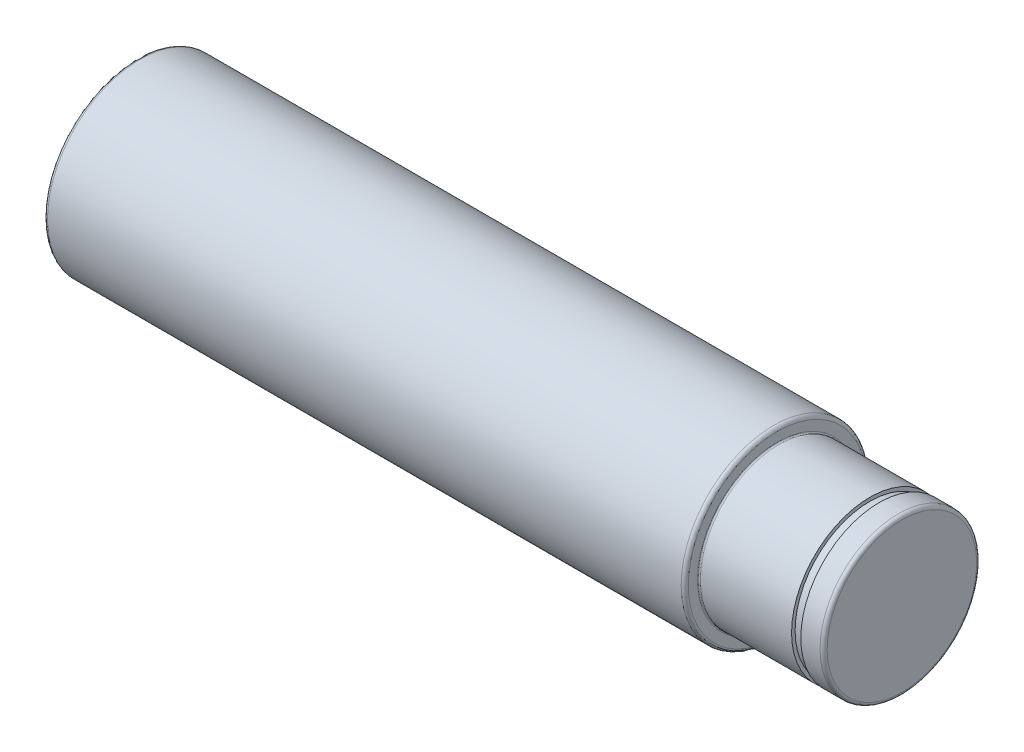
SolidWorks part; units mm, degrees
ref_plane "Plane1" through (0, 0, 0) normal (0, 0, 1) x (1, 0, 0)
ref_plane "Plane2" through (0, 0, 0) normal (0, 1, 0) x (1, 0, 0)
ref_plane "Plane3" through (0, 0, 0) normal (1, 0, 0) x (0, 0, -1)
sketch "Sketch1" plane through (0, 0, 0) normal (0, 0, 1) x (1, 0, 0)
  line L0 (0, 0) -> (0, 12.5)
  line L1 (0.5, 13) -> (89.5, 13)
  line L2 (90, 12.5) -> (90, 11.2)
  line L3 (90.2, 11) -> (103, 11)
  line L4 (103, 11) -> (103, 10.5)
  line L5 (103, 10.5) -> (104.3, 10.5)
  line L6 (104.3, 10.5) -> (104.3, 11)
  line L7 (104.3, 11) -> (107, 11)
  line L8 (107.5, 10.5) -> (107.5, 0)
  line L9 (0, 0) -> (144.9798, 0) construction
  line L10 (0, 0) -> (107.5, 0)
  arc A0 (107, 11) -> (107.5, 10.5) centre (107, 10.5) cw
  arc A1 (89.5, 13) -> (90, 12.5) centre (89.5, 12.5) cw
  arc A2 (0, 12.5) -> (0.5, 13) centre (0.5, 12.5) cw
  arc A3 (90, 11.2) -> (90.2, 11) centre (90.2, 11.2) ccw
  dimension "D10" = 0.5
  dimension "D11" = 0.2
  dimension "D1" = 22
  dimension "D2" = 21
  dimension "D3" = 4.5
  dimension "D4" = 1.3
  dimension "D5" = 17.5
  dimension "D6" = 13
  dimension "D7" = 107.5
  dimension "D8" = 90
  dimension "D9" = 26
revolve "Revolve1" add sketch "Sketch1" angle 360 about L9
